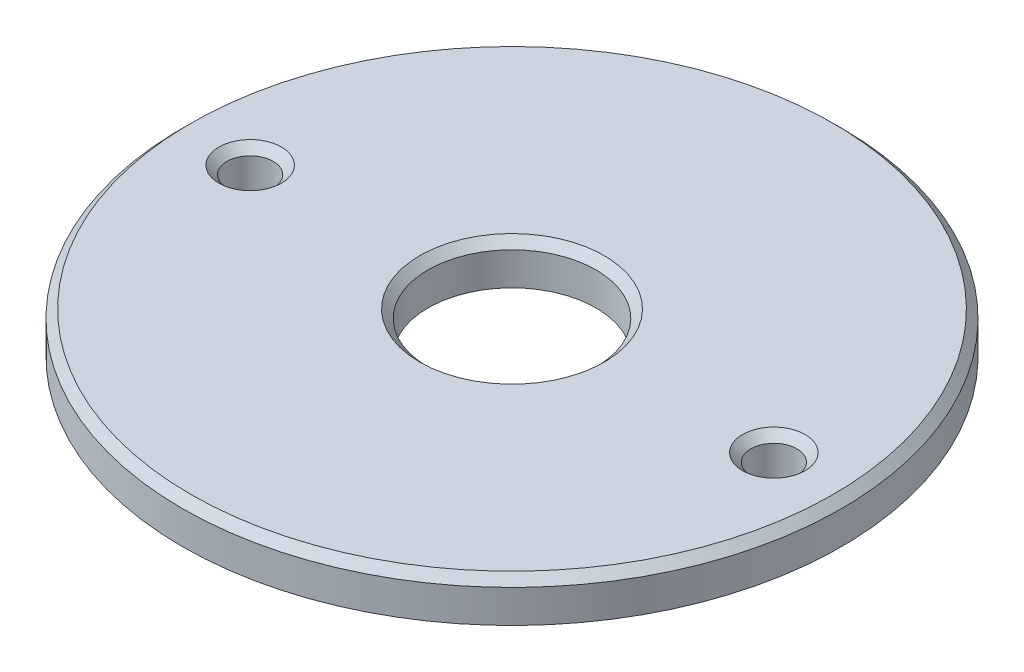
SolidWorks part; units mm, degrees
ref_plane "Front Plane" through (0, 0, 0) normal (0, 0, 1) x (1, 0, 0)
ref_plane "Top Plane" through (0, 0, 0) normal (0, 1, 0) x (1, 0, 0)
ref_plane "Right Plane" through (0, 0, 0) normal (1, 0, 0) x (0, 0, -1)
sketch "Sketch1" plane through (0, 0, 0) normal (0, 1, 0) x (1, 0, 0)
  line L0 (-39.37, -0.9923) -> (39.37, 0.9923) construction
  circle A0 centre (0, 0) radius 50.8
  circle A1 centre (-39.37, -0.9923) radius 3.556
  circle A2 centre (0, 0) radius 12.954
  circle A4 centre (39.37, 0.9923) radius 3.556
  point P8 (0, 0)
  point P9 (0, 0)
  dimension "D1" = 101.6
  dimension "D2" = 7.112
  dimension "D3" = 25.908
  dimension "D5" = 7.112
  dimension "D4" = 78.74
  dimension "D6" = 39.37
  dimension "D7" = 39.37
extrude "Boss-Extrude1" add sketch "Sketch1" along normal blind 6.35
chamfer "Chamfer1" distance 1.27 angle 45 4 edges at (39.37, 6.35, 2.5637) (0, 6.35, 12.954) (0, 6.35, 50.8) (-39.37, 6.35, 4.5483)
